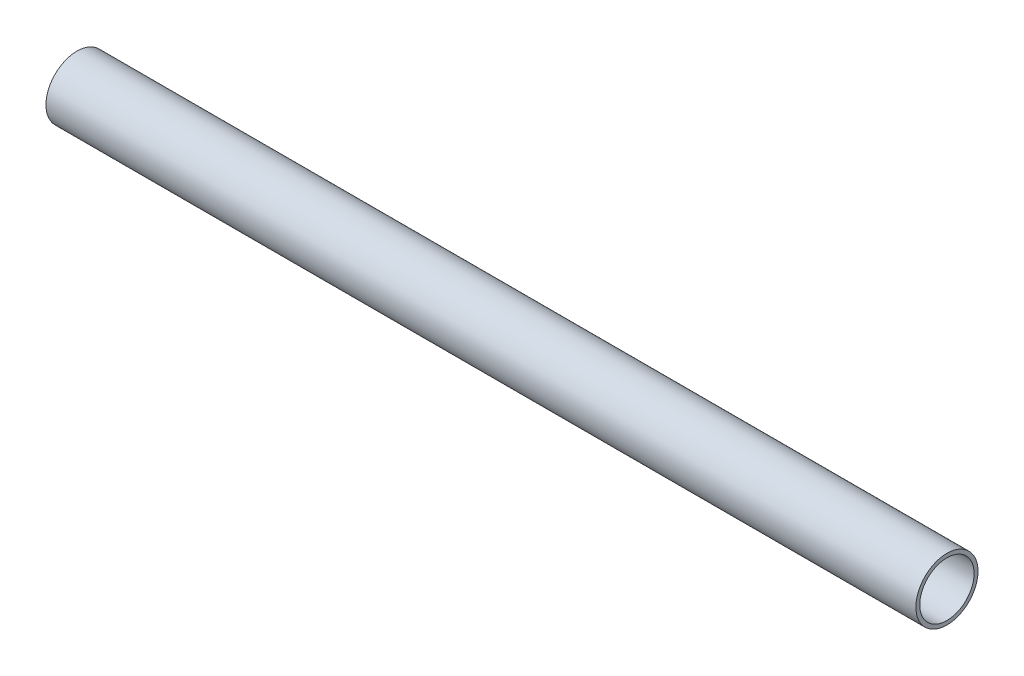
SolidWorks part; units mm, degrees
ref_plane "Front Plane" through (0, 0, 0) normal (0, 0, 1) x (1, 0, 0)
ref_plane "Top Plane" through (0, 0, 0) normal (0, 1, 0) x (1, 0, 0)
ref_plane "Right Plane" through (0, 0, 0) normal (1, 0, 0) x (0, 0, -1)
sketch "Sketch1" plane through (0, 0, 0) normal (1, 0, 0) x (0, 0, -1)
  circle A0 centre (0, 0) radius 12.7
  circle A1 centre (0, 0) radius 11.1125
  dimension "D1" = 25.4
  dimension "D2" = 1.5875
extrude "Boss-Extrude1" add sketch "Sketch1" along normal blind 355.6
